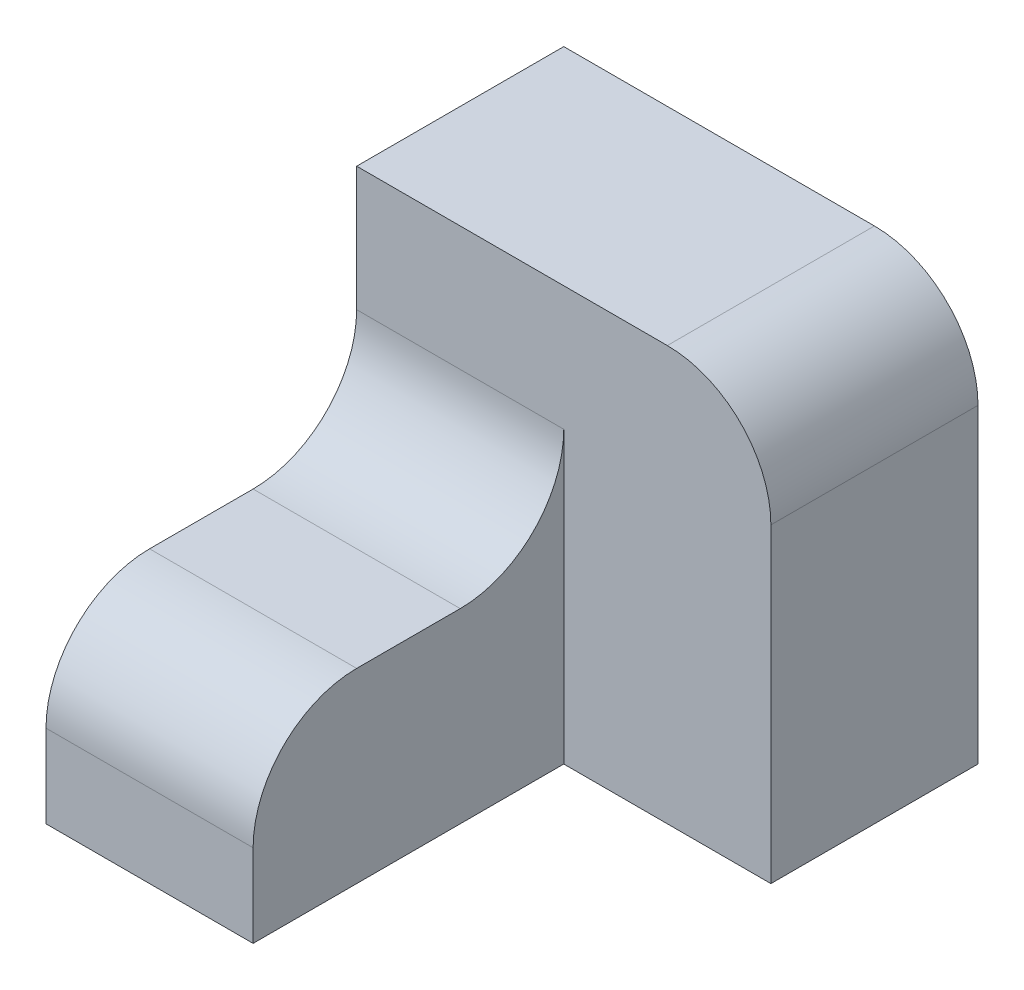
SolidWorks part; units mm, degrees
ref_plane "Front Plane" through (0, 0, 0) normal (0, 0, 1) x (1, 0, 0)
ref_plane "Top Plane" through (0, 0, 0) normal (0, 1, 0) x (1, 0, 0)
ref_plane "Right Plane" through (0, 0, 0) normal (1, 0, 0) x (0, 0, -1)
sketch "Sketch1" plane through (0, 0, 0) normal (0, 0, 1) x (1, 0, 0)
  line L1 (-30, -18) -> (-10, -18)
  line L2 (-10, -18) -> (-10, 0)
  line L3 (-10, 0) -> (-30, 0)
  line L4 (-30, 0) -> (-30, -18)
  dimension "D1" = 20
  dimension "Width" = 18
extrude "Boss-Extrude1" add sketch "Sketch1" along normal blind 30
sketch "Sketch2" plane through (0, 0, 0) normal (0, 0, 1) x (1, 0, 0)
  line L1 (-30, -18) -> (10, -18)
  line L2 (10, -18) -> (10, 22)
  line L3 (10, 22) -> (-30, 22)
  line L4 (-30, 22) -> (-30, -18)
  dimension "D1" = 40
  dimension "Width" = 40
extrude "Boss-Extrude2" add sketch "Sketch2" against normal blind 20
fillet "Fillet1" radius 10 3 edges at (-20, 0, 0) (10, 22, -10) (-20, 0, 30)
